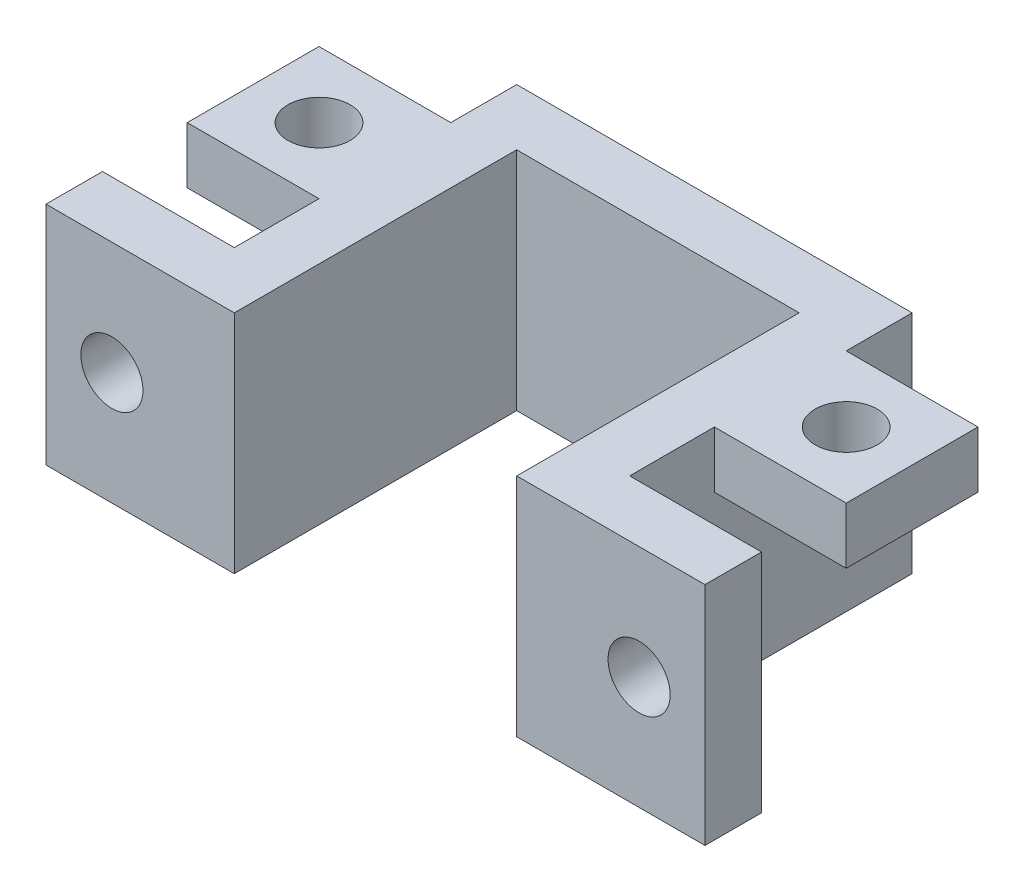
SolidWorks part; units mm, degrees
ref_plane "Front Plane" through (0, 0, 0) normal (0, 0, 1) x (1, 0, 0)
ref_plane "Top Plane" through (0, 0, 0) normal (0, 1, 0) x (1, 0, 0)
ref_plane "Right Plane" through (0, 0, 0) normal (1, 0, 0) x (0, 0, -1)
sketch "Sketch1" plane through (0, 0, 0) normal (0, 1, 0) x (1, 0, 0)
  line L0 (0, 0) -> (7.5, 0) construction
  line L1 (0, 0) -> (0, 7.5) construction
  line L2 (0, 0) -> (-7.5, 0) construction
  line L3 (7.5, -7.5) -> (7.5, 7.5)
  line L4 (-7.5, 7.5) -> (7.5, 7.5)
  line L5 (-7.5, -7.5) -> (-7.5, 7.5)
  line L9 (-10.5, 10.5) -> (10.5, 10.5)
  line L11 (-7.5, -7.5) -> (-17.5, -7.5)
  line L12 (7.5, -7.5) -> (17.5, -7.5)
  line L13 (-17.5, -7.5) -> (-17.5, -4.5)
  line L14 (-17.5, -4.5) -> (-10.5, -4.5)
  line L15 (-10.5, -4.5) -> (-10.5, 10.5)
  line L16 (17.5, -7.5) -> (17.5, -4.5)
  line L17 (17.5, -4.5) -> (10.5, -4.5)
  line L18 (10.5, -4.5) -> (10.5, 10.5)
  point P7 (7.5, 0)
  point P10 (0, 7.5)
  point P13 (-7.5, 0)
  dimension "D1" = 7.5
  dimension "D2" = 3
  dimension "D3" = 10
  dimension "D4" = 3
  dimension "D5" = 3
  dimension "D6" = 3
extrude "Boss-Extrude1" add sketch "Sketch1" along normal blind 12
sketch "Sketch2" plane through (0, 0, 7.5) normal (0, 0, 1) x (1, 0, 0)
  circle A0 centre (-14, 6) radius 1.65
  circle A1 centre (14, 6) radius 1.65
  dimension "D1" = 3.3
  dimension "D2" = 6
  dimension "D3" = 28
  dimension "D4" = 14
  dimension "D5" = 6
extrude "Cut-Extrude1" cut sketch "Sketch2" against normal blind 12
sketch "Sketch3" plane through (0, 12, 0) normal (0, 1, 0) x (1, 0, 0)
  line L0 (-10.5, 10.5) -> (-10.5, -4.5) construction
  line L1 (-10.5, 0) -> (-17.5, 0)
  line L2 (-10.5, 0) -> (-10.5, 7)
  line L3 (-10.5, 7) -> (-17.5, 7)
  line L4 (-17.5, 0) -> (-17.5, 7)
  line L5 (10.5, -4.5) -> (10.5, 10.5) construction
  line L6 (10.5, 0) -> (17.5, 0)
  line L7 (10.5, 0) -> (10.5, 7)
  line L8 (10.5, 7) -> (17.5, 7)
  line L9 (17.5, 0) -> (17.5, 7)
  circle A0 centre (-14, 3.5) radius 1.65
  circle A1 centre (14, 3.5) radius 1.65
  dimension "D3" = 3.3
  dimension "D4" = 3.5
  dimension "D5" = 3.5
  dimension "D6" = 3.5
  dimension "D7" = 3.5
  dimension "D1" = 7
  dimension "D2" = 7
extrude "Boss-Extrude2" add sketch "Sketch3" against normal blind 3
